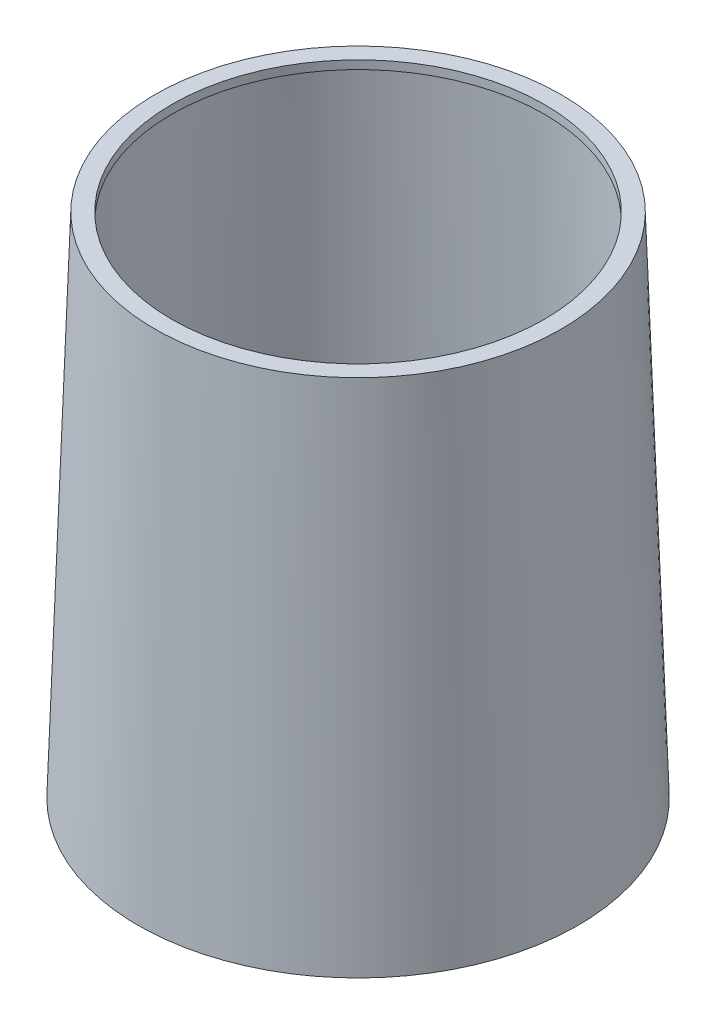
SolidWorks part; units mm, degrees
ref_plane "Front Plane" through (0, 0, 0) normal (0, 0, 1) x (1, 0, 0)
ref_plane "Top Plane" through (0, 0, 0) normal (0, 1, 0) x (1, 0, 0)
ref_plane "Right Plane" through (0, 0, 0) normal (1, 0, 0) x (0, 0, -1)
sketch "Sketch3" plane through (0, 0, 0) normal (0, 0, 1) x (1, 0, 0)
  line L0 (0, 0) -> (13, 0)
  line L1 (0, 0) -> (0, 30)
  line L2 (0, 30) -> (12, 30)
  line L3 (12, 30) -> (13, 0)
  point P3 (17, 0)
  dimension "D1" = 12
  dimension "D2" = 13
  dimension "D3" = 30
revolve "Revolve1" add sketch "Sketch3" angle 360 about L1
sketch "Sketch6" plane through (0, 30, 0) normal (0, 1, 0) x (1, 0, 0)
  circle A0 centre (0, 0) radius 11
  circle A1 centre (0, 0) radius 12 construction
  dimension "D1" = 1
extrude "Cut-Extrude1" cut sketch "Sketch6" against normal blind 30
sketch "Sketch7" plane through (0, 0, 0) normal (0, 0, 1) x (1, 0, 0)
  line L0 (8.9856, 29.5) -> (9.6275, 0.5)
  line L1 (9.6275, 0.5) -> (12.4831, 0.5)
  line L2 (12.4831, 0.5) -> (11.5164, 29.5)
  line L3 (11.5164, 29.5) -> (8.9856, 29.5)
  line L4 (13, 0) -> (12, 30) construction
  line L6 (-13, 0) -> (13, 0) construction
  line L7 (11, 30) -> (-11, 30) construction
  line L8 (0, 0) -> (0, 24.971) construction
  dimension "D1" = 0.5
  dimension "D2" = 0.5
  dimension "D3" = 0.5
revolve "Cut-Revolve1" cut sketch "Sketch7" angle 360 about L8
sketch "Sketch8" plane through (0, 0, 0) normal (0, -1, 0) x (-1, 0, 0)
  circle A0 centre (0, 0) radius 11.5
  circle A1 centre (0, 0) radius 12.5
  circle A2 centre (0, 0) radius 13 construction
  circle A3 centre (0, 0) radius 11 construction
  dimension "D1" = 0.5
  dimension "D2" = 0.5
extrude "Cut-Extrude3" cut sketch "Sketch8" against normal blind 0.5
